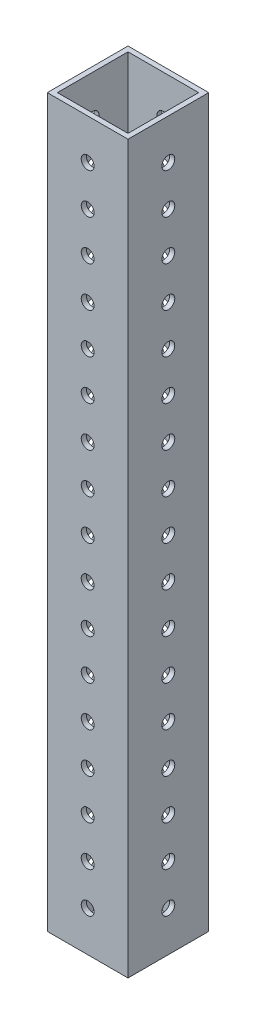
SolidWorks part; units mm, degrees
material "6061 Alloy"
ref_plane "Front Plane" through (0, 0, 0) normal (0, 0, 1) x (1, 0, 0)
ref_plane "Top Plane" through (0, 0, 0) normal (0, 1, 0) x (1, 0, 0)
ref_plane "Right Plane" through (0, 0, 0) normal (1, 0, 0) x (0, 0, -1)
sketch "Sketch1" plane through (0, 0, 0) normal (0, 1, 0) x (1, 0, 0)
  line L0 (1.5875, 1.5875) -> (1.5875, 23.8125)
  line L1 (0, 0) -> (25.4, 0)
  line L2 (0, 0) -> (0, 25.4)
  line L3 (0, 25.4) -> (25.4, 25.4)
  line L4 (25.4, 0) -> (25.4, 25.4)
  line L5 (1.5875, 23.8125) -> (23.8125, 23.8125)
  line L6 (23.8125, 1.5875) -> (23.8125, 23.8125)
  line L7 (1.5875, 1.5875) -> (23.8125, 1.5875)
  dimension "D2" = 25.4
  dimension "D3" = 25.4
  dimension "D1" = 1.5875
extrude "Boss-Extrude1" add sketch "Sketch1" along normal blind 228.6
sketch "Sketch2" plane through (0, 0, 0) normal (0, 0, 1) x (1, 0, 0)
  line L0 (0, 0) -> (25.4, 0) construction
  line L1 (0, 228.6) -> (0, 0) construction
  circle A0 centre (12.7, 12.7) radius 2.0193
  circle A1 centre (12.7, 25.4) radius 2.0193
  circle A2 centre (12.7, 38.1) radius 2.0193
  circle A3 centre (12.7, 50.8) radius 2.0193
  circle A4 centre (12.7, 63.5) radius 2.0193
  circle A5 centre (12.7, 76.2) radius 2.0193
  circle A6 centre (12.7, 88.9) radius 2.0193
  circle A7 centre (12.7, 101.6) radius 2.0193
  circle A8 centre (12.7, 114.3) radius 2.0193
  circle A9 centre (12.7, 127) radius 2.0193
  circle A10 centre (12.7, 139.7) radius 2.0193
  circle A11 centre (12.7, 152.4) radius 2.0193
  circle A12 centre (12.7, 165.1) radius 2.0193
  circle A13 centre (12.7, 177.8) radius 2.0193
  circle A14 centre (12.7, 190.5) radius 2.0193
  circle A15 centre (12.7, 203.2) radius 2.0193
  circle A16 centre (12.7, 215.9) radius 2.0193
  dimension "D3" = 4.0386
  dimension "D1" = 12.7
  dimension "D2" = 12.7
  dimension "D5" = 12.7
  dimension "D4" = 17
extrude "Cut-Extrude1" cut sketch "Sketch2" against normal through all
sketch "Sketch3" plane through (25.4, 0, 0) normal (1, 0, 0) x (0, 0, -1)
  line L2 (25.4, 228.6) -> (25.4, 0) construction
  line L3 (0, 0) -> (25.4, 0) construction
  circle A0 centre (12.7, 12.7) radius 2.0193
  circle A1 centre (12.7, 25.4) radius 2.0193
  circle A2 centre (12.7, 38.1) radius 2.0193
  circle A3 centre (12.7, 50.8) radius 2.0193
  circle A4 centre (12.7, 63.5) radius 2.0193
  circle A5 centre (12.7, 76.2) radius 2.0193
  circle A6 centre (12.7, 88.9) radius 2.0193
  circle A7 centre (12.7, 101.6) radius 2.0193
  circle A8 centre (12.7, 114.3) radius 2.0193
  circle A9 centre (12.7, 127) radius 2.0193
  circle A10 centre (12.7, 139.7) radius 2.0193
  circle A11 centre (12.7, 152.4) radius 2.0193
  circle A12 centre (12.7, 165.1) radius 2.0193
  circle A13 centre (12.7, 177.8) radius 2.0193
  circle A14 centre (12.7, 190.5) radius 2.0193
  circle A15 centre (12.7, 203.2) radius 2.0193
  circle A16 centre (12.7, 215.9) radius 2.0193
  dimension "D3" = 4.0386
  dimension "D1" = 12.7
  dimension "D2" = 12.7
  dimension "D5" = 12.7
  dimension "D4" = 17
extrude "Cut-Extrude2" cut sketch "Sketch3" against normal through all
equation "\"Bar thickness\" = 0.0625"
equation "\"Length\" = 9"
equation "\"D1@Sketch1\"=\"Bar thickness\""
equation "\"D1@Boss-Extrude1\"=\"Length\""
equation "\"D4@Sketch2\"= \"Length\" * 2 -1"
equation "\"D4@Sketch3\"= \"Length\" * 2 -1"
